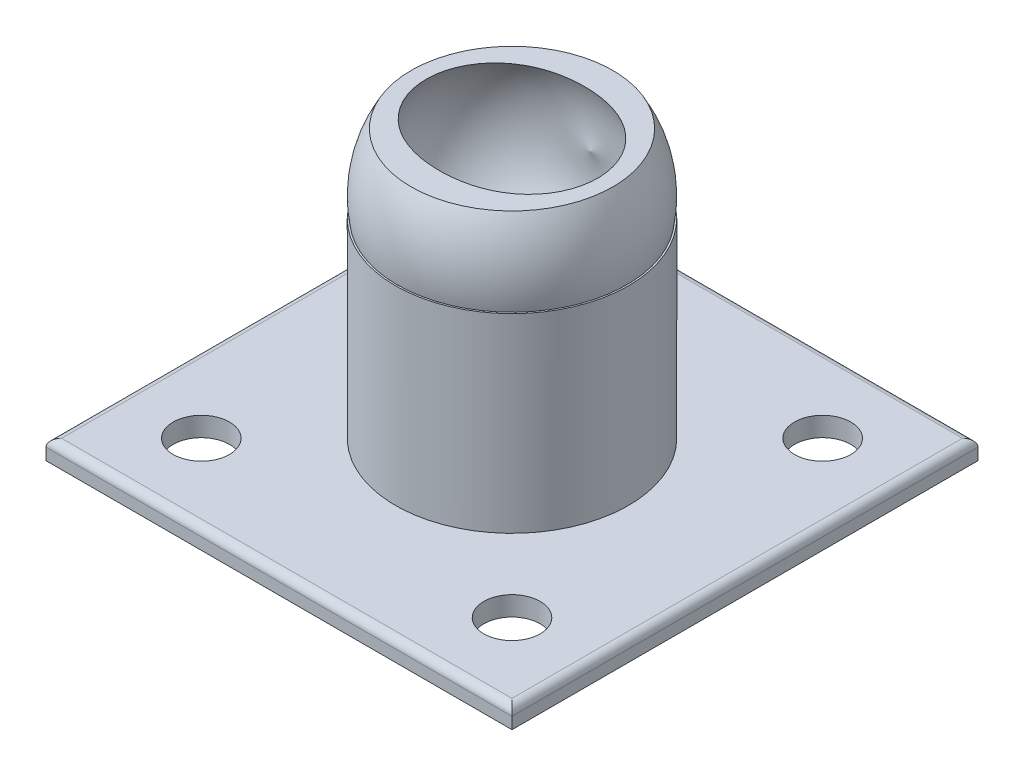
SolidWorks part; units mm, degrees
ref_plane "Plan de face" through (0, 0, 0) normal (0, 0, 1) x (1, 0, 0)
ref_plane "Plan de dessus" through (0, 0, 0) normal (0, 1, 0) x (1, 0, 0)
ref_plane "Plan de droite" through (0, 0, 0) normal (1, 0, 0) x (0, 0, -1)
sketch "Esquisse3" plane through (0, 0, 0) normal (0, 1, 0) x (1, 0, 0)
  line L1 (60, 60) -> (-60, 60)
  line L2 (60, 60) -> (60, -60)
  line L3 (60, -60) -> (-60, -60)
  line L4 (-60, 60) -> (-60, -60)
  line L5 (60, 60) -> (-60, -60) construction
  line L6 (60, -60) -> (-60, 60) construction
  point P0 (0, 0)
  dimension "D1" = 120
  dimension "D2" = 120
extrude "Boss.-Extru.2" add sketch "Esquisse3" along normal blind 5
sketch "Esquisse5" plane through (0, 5, 0) normal (0, 1, 0) x (1, 0, 0)
  line L0 (60, 60) -> (-60, 60) construction
  line L1 (-60, 60) -> (-60, -60) construction
  circle A0 centre (-40, 40) radius 7.25
  dimension "D1" = 14.5
  dimension "D2" = 20
  dimension "D3" = 20
extrude "Enlèv. mat.-Extru.1" cut sketch "Esquisse5" against normal blind 5
sketch "Esquisse6" plane through (0, 0, 0) normal (0, 1, 0) x (1, 0, 0)
  line L0 (-1000, 0) -> (49000, 0) construction
  line L1 (0, -1000) -> (0, 49000) construction
  circle A1 centre (-40, 40) radius 7.25 construction
  circle A2 centre (-40, 40) radius 7.25
  circle A3 centre (40, 40) radius 7.25
  circle A4 centre (-40, -40) radius 7.25
  circle A5 centre (40, -40) radius 7.25
extrude "Enlèv. mat.-Extru.7" cut sketch "Esquisse6" along normal blind 5
fillet "Congé4" radius 2 4 edges at (60, 5, 0) (0, 5, -60) (-60, 5, 0) (0, 5, 60)
sketch "Esquisse19" plane through (0, 0, 0) normal (1, 0, 0) x (0, 0, -1)
  line L0 (0, -1000) -> (0, 49000) construction
  line L1 (30, 59.0365) -> (-30, 59.0365)
  arc A0 (30, 59.0365) -> (-30, 59.0365) centre (0, 59.0365) cw
  point P6 (0, 0)
  point P7 (0, 0)
  dimension "D1" = 60
revolve "Révolution2" add sketch "Esquisse19" angle 360 about L1
sketch "Esquisse20" plane through (0, 0, 0) normal (1, 0, 0) x (0, 0, -1)
  line L0 (0, -1000) -> (0, 49000) construction
  line L1 (-20, 59.0365) -> (20, 59.0365)
  arc A2 (-20, 59.0365) -> (20, 59.0365) centre (0, 64.8999) cw
  circle A3 centre (0, 59.0365) radius 30 construction
  dimension "D1" = 40
  dimension "D2" = 0
sketch "Esquisse24" plane through (0, 5, 0) normal (0, 1, 0) x (1, 0, 0)
  circle A0 centre (0, 0) radius 30
extrude "Boss.-Extru.6" add sketch "Esquisse24" along normal blind 49
revolve "Enlèvement de matière-Révolution5" cut sketch "Esquisse20" angle 360 about L1
sketch "Esquisse25" plane through (0, 0, 0) normal (0, 0, 1) x (1, 0, 0)
  line L1 (29.2864, 97.717) -> (-29.2864, 97.717)
  line L2 (29.2864, 97.717) -> (29.2864, 74.0471)
  line L3 (29.2864, 74.0471) -> (-29.2864, 74.0471)
  line L4 (-29.2864, 97.717) -> (-29.2864, 74.0471)
  line L5 (29.2864, 97.717) -> (-29.2864, 74.0471) construction
  line L6 (29.2864, 74.0471) -> (-29.2864, 97.717) construction
  point P0 (0, 85.8821)
extrude "Enlèv. mat.-Extru.9" cut sketch "Esquisse25" against normal blind 39 and the other way blind 49
